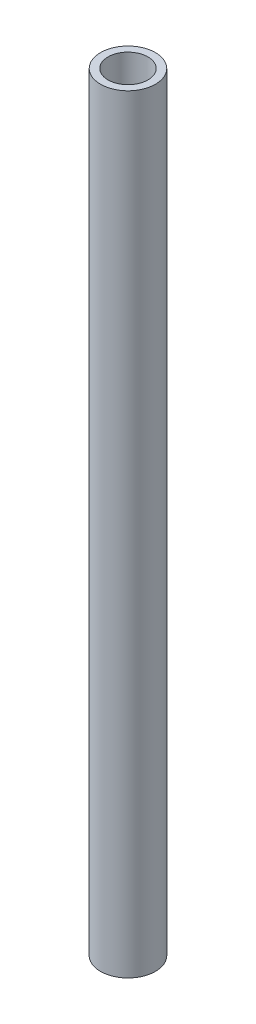
SolidWorks part; units mm, degrees
ref_plane "Front Plane" through (0, 0, 0) normal (0, 0, 1) x (1, 0, 0)
ref_plane "Top Plane" through (0, 0, 0) normal (0, 1, 0) x (1, 0, 0)
ref_plane "Right Plane" through (0, 0, 0) normal (1, 0, 0) x (0, 0, -1)
sketch "Sketch1" plane through (0, 0, 0) normal (0, 1, 0) x (1, 0, 0)
  circle A0 centre (0, 0) radius 10.715
  circle A1 centre (0, 0) radius 7.8
  dimension "D1" = 21.43
  dimension "D2" = 15.6
extrude "Boss-Extrude1" add sketch "Sketch1" along normal blind 300
